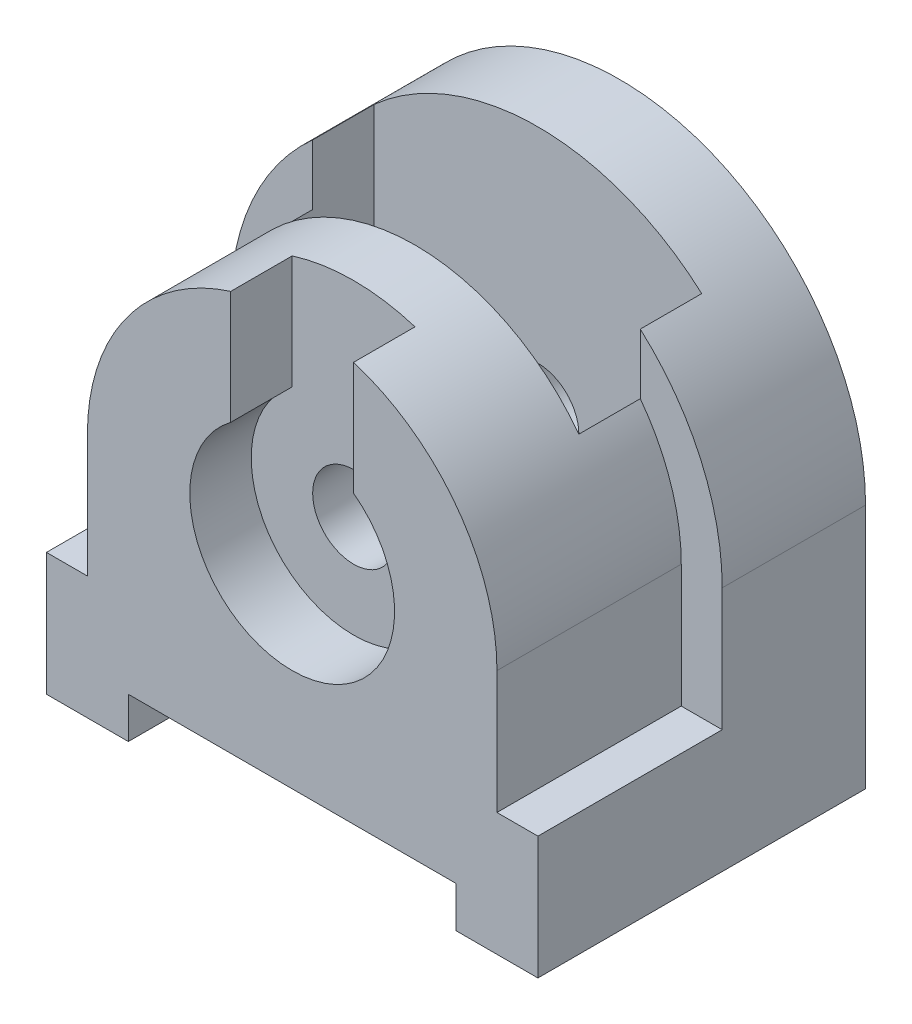
SolidWorks part; units mm, degrees
ref_plane "Front Plane" through (0, 0, 0) normal (0, 0, 1) x (1, 0, 0)
ref_plane "Top Plane" through (0, 0, 0) normal (0, 1, 0) x (1, 0, 0)
ref_plane "Right Plane" through (0, 0, 0) normal (1, 0, 0) x (0, 0, -1)
sketch "Sketch1" plane through (0, 0, 0) normal (0, 0, 1) x (1, 0, 0)
  line L1 (0, 0) -> (120, 0)
  line L2 (0, 0) -> (0, 60)
  line L3 (0, 60) -> (120, 60)
  line L4 (120, 0) -> (120, 60)
  dimension "D1" = 120
  dimension "D2" = 60
extrude "Boss-Extrude2" add sketch "Sketch1" along normal blind 80
sketch "Sketch2" plane through (0, 0, 80) normal (0, 0, 1) x (1, 0, 0)
  line L0 (0, 0) -> (120, 0) construction
  line L1 (20, 0) -> (100, 0)
  line L2 (20, 0) -> (20, 10)
  line L3 (20, 10) -> (100, 10)
  line L4 (100, 0) -> (100, 10)
  dimension "D1" = 10
  dimension "D2" = 20
  dimension "D3" = 20
extrude "Cut-Extrude1" cut sketch "Sketch2" against normal blind 80
sketch "Sketch3" plane through (0, 0, 80) normal (0, 0, 1) x (1, 0, 0)
  line L0 (120, 60) -> (0, 60) construction
  line L1 (0, 60) -> (120, 60)
  arc A0 (120, 60) -> (0, 60) centre (60, 60) ccw
extrude "Boss-Extrude3" add sketch "Sketch3" against normal blind 80
sketch "Sketch4" plane through (0, 0, 80) normal (0, 0, 1) x (1, 0, 0)
  circle A0 centre (60, 60) radius 10
  dimension "D1" = 20
extrude "Cut-Extrude2" cut sketch "Sketch4" against normal blind 80
sketch "Sketch5" plane through (0, 0, 80) normal (0, 0, 1) x (1, 0, 0)
  line L0 (45, 80) -> (45, 118.0948)
  line L1 (75, 80) -> (75, 118.0948)
  arc A0 (75, 80) -> (45, 80) centre (60, 60) cw
  arc A1 (120, 60) -> (0, 60) centre (60, 60) ccw construction
  arc A2 (75, 118.0948) -> (45, 118.0948) centre (60, 63.3155) ccw
  dimension "D1" = 25
  dimension "D4" = 56.7959
  dimension "D2" = 15
  dimension "D3" = 15
extrude "Cut-Extrude3" cut sketch "Sketch5" against normal blind 15
sketch "Sketch6" plane through (0, 0, 80) normal (0, 0, 1) x (1, 0, 0)
  line L0 (10, 60) -> (10, 30)
  line L2 (10, 30) -> (0, 30)
  line L5 (0, 30) -> (0, 60)
  line L6 (110, 60) -> (110, 30)
  line L7 (110, 30) -> (120, 30)
  line L8 (120, 0) -> (120, 60) construction
  line L9 (120, 30) -> (120, 60)
  line L10 (20, 104.7214) -> (20, 90)
  line L11 (100, 104.7214) -> (100, 90)
  arc A0 (110, 60) -> (10, 60) centre (60, 60) ccw
  arc A1 (120, 60) -> (0, 60) centre (60, 60) ccw
  arc M3 (45, 118.0948) -> (0, 60) centre (60, 60) ccw
  line M4 (0, 60) -> (0, 0)
  line M10 (120, 0) -> (120, 60)
  arc M11 (120, 60) -> (75, 118.0948) centre (60, 60) ccw
  dimension "D2" = 50
  dimension "D1" = 10
  dimension "D3" = 10
  dimension "D4" = 30
  dimension "D5" = 30
  dimension "D6" = 10
  dimension "D7" = 20
  dimension "D8" = 20
extrude "Cut-Extrude4" cut sketch "Sketch6" against normal blind 45 contours A0 L10 L2 L0 M3 M4 | A0 L6 L7 L11 M10 M11
sketch "Sketch7" plane through (0, 0, 80) normal (0, 0, 1) x (1, 0, 0)
  line L0 (0, 60) -> (10, 60)
  line L1 (110, 60) -> (120, 60)
  arc A0 (110, 60) -> (10, 60) centre (60, 60) ccw
  arc A1 (110, 60) -> (100, 90) centre (60, 60) ccw construction
  arc A2 (120, 60) -> (0, 60) centre (60, 60) ccw
  dimension "D1" = 60
  dimension "D2" = 10
  dimension "D3" = 60
  dimension "D4" = 10
  dimension "D5" = 60
  dimension "D6" = 60
extrude "Cut-Extrude5" cut sketch "Sketch7" against normal blind 30
ref_plane "Plane1" through (0, 0, 20) normal (0, 0, 1) x (1, 0, 0)
ref_plane "Plane2" through (100, 90, 50) normal (0.6, -0.8, 0) x (-0.8, -0.6, 0)
sketch "Sketch13" plane through (0, 10, 0) normal (0, -1, 0) x (-1, 0, 0)
  line L0 (-100, 0) -> (-100, -80) construction
  line L1 (-100, -20) -> (-20, -20)
  line L2 (-100, -20) -> (-100, -50)
  line L3 (-100, -50) -> (-20, -50)
  line L4 (-20, -20) -> (-20, -50)
  line L5 (-20, 0) -> (-20, -80) construction
  dimension "D1" = 30
  dimension "D2" = 20
extrude "Cut-Extrude12" cut sketch "Sketch13" against normal blind 950
ref_plane "Plane3" through (0, 0, 20) normal (0, 0, 1) x (1, 0, 0)
sketch "Sketch14" plane through (0, 0, 20) normal (0, 0, 1) x (1, 0, 0)
  line L0 (20, 10) -> (100, 10) construction
  line L1 (65, 10) -> (55, 10)
  line L2 (65, 10) -> (65, 35)
  line L3 (65, 35) -> (55, 35)
  line L4 (55, 10) -> (55, 35)
  dimension "D1" = 10
  dimension "D2" = 55
  dimension "D3" = 25
extrude "Boss-Extrude4" add sketch "Sketch14" along normal blind 30
